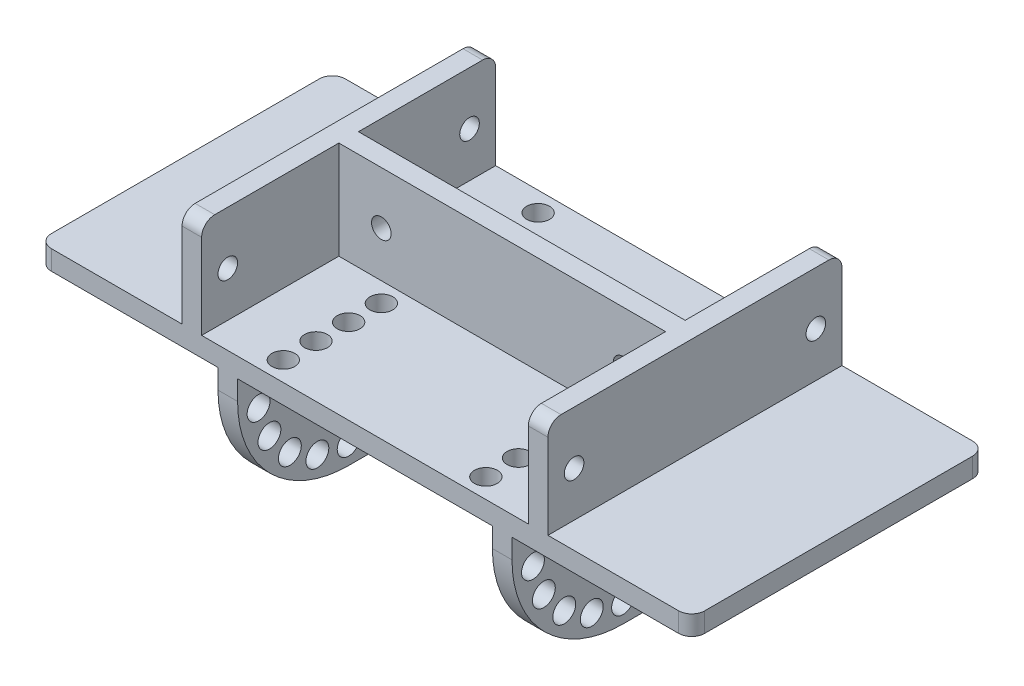
SolidWorks part; units mm, degrees
ref_plane "Front Plane" through (0, 0, 0) normal (0, 0, 1) x (1, 0, 0)
ref_plane "Top Plane" through (0, 0, 0) normal (0, 1, 0) x (1, 0, 0)
ref_plane "Right Plane" through (0, 0, 0) normal (1, 0, 0) x (0, 0, -1)
sketch "Sketch1" plane through (0, 0, 0) normal (0, 1, 0) x (1, 0, 0)
  line L1 (-50, 22.5) -> (50, 22.5)
  line L2 (-50, 22.5) -> (-50, -22.5)
  line L3 (-50, -22.5) -> (50, -22.5)
  line L4 (50, 22.5) -> (50, -22.5)
  line L5 (-50, 22.5) -> (50, -22.5) construction
  line L6 (-50, -22.5) -> (50, 22.5) construction
  point P0 (0, 0)
  dimension "D1" = 100
  dimension "D2" = 45
extrude "Boss-Extrude1" add sketch "Sketch1" along normal blind 3
sketch "Sketch2" plane through (0, 3, 0) normal (0, 1, 0) x (1, 0, 0)
  line L0 (50, 22.5) -> (-50, 22.5) construction
  line L1 (-28, 22.5) -> (-25, 22.5)
  line L2 (-28, 22.5) -> (-28, -22.5)
  line L3 (-28, -22.5) -> (-25, -22.5)
  line L4 (-25, 22.5) -> (-25, -22.5)
  line L5 (-50, -22.5) -> (50, -22.5) construction
  line L6 (-50, 22.5) -> (-50, -22.5) construction
  line L7 (25, 22.5) -> (28, 22.5)
  line L8 (25, 22.5) -> (25, -22.5)
  line L9 (25, -22.5) -> (28, -22.5)
  line L10 (28, 22.5) -> (28, -22.5)
  line L11 (50, -22.5) -> (50, 22.5) construction
  line L13 (-25, 1.5) -> (25, 1.5)
  line L14 (-25, 1.5) -> (-25, -1.5)
  line L15 (-25, -1.5) -> (25, -1.5)
  line L16 (25, 1.5) -> (25, -1.5)
  line M8 (50, 22.5) -> (-50, 22.5)
  line M10 (-50, -22.5) -> (50, -22.5)
  dimension "D1" = 3
  dimension "D2" = 3
  dimension "D3" = 22
  dimension "D4" = 22
  dimension "D5" = 3
  dimension "D6" = 21
extrude "Boss-Extrude2" add sketch "Sketch2" along normal blind 15 contours L4 L15 L8 L13 | L10 L8 M8 M10
sketch "Sketch4" plane through (-28, 0, 0) normal (-1, 0, 0) x (0, 0, 1)
  line L0 (0, 0) -> (0, 9.8851) construction
  line L1 (-18.5, 9.8851) -> (18.5, 9.8851) construction
  circle A0 centre (-18.5, 9.8851) radius 1.5
  circle A1 centre (18.5, 9.8851) radius 1.5
  point P6 (0, 9.8851)
  dimension "D2" = 3
  dimension "D3" = 3
  dimension "D1" = 37
extrude "Cut-Extrude1" cut sketch "Sketch4" against normal through all
sketch "Sketch5" plane through (0, 0, 1.5) normal (0, 0, 1) x (1, 0, 0)
  line L0 (0, 0) -> (0, 9.9635) construction
  line L1 (-18.5, 9.9635) -> (18.5, 9.9635) construction
  circle A0 centre (-18.5, 9.9635) radius 1.5
  circle A1 centre (18.5, 9.9635) radius 1.5
  point P5 (0, 9.9635)
  dimension "D2" = 3
  dimension "D3" = 3
  dimension "D1" = 37
extrude "Cut-Extrude2" cut sketch "Sketch5" against normal through all
fillet "Fillet1" radius 2 8 edges at (-26.5, 18, 22.5) (26.5, 18, 22.5) (26.5, 18, -22.5) (-26.5, 18, -22.5) (50, 1.5, 22.5) (-50, 1.5, 22.5) (-50, 1.5, -22.5) (50, 1.5, -22.5)
sketch "Sketch6" plane through (0, 0, 0) normal (0, -1, 0) x (1, 0, 0)
  line L0 (-19.5, 0) -> (19.5, 0) construction
  line L1 (48, -22.5) -> (-48, -22.5) construction
  line L2 (-19.5, 22.5) -> (-22.5, 22.5)
  line L3 (-19.5, 22.5) -> (-19.5, -22.5)
  line L4 (-19.5, -22.5) -> (-22.5, -22.5)
  line L5 (-22.5, 22.5) -> (-22.5, -22.5)
  line L7 (19.5, 22.5) -> (22.5, 22.5)
  line L8 (19.5, 22.5) -> (19.5, -22.5)
  line L9 (19.5, -22.5) -> (22.5, -22.5)
  line L10 (22.5, 22.5) -> (22.5, -22.5)
  point P3 (0, 0)
  point P14 (0, 0)
  dimension "D1" = 39
  dimension "D2" = 45
  dimension "D3" = 3
  dimension "D4" = 3
  dimension "D5" = 45
extrude "Boss-Extrude3" add sketch "Sketch6" along normal blind 20
fillet "Fillet2" radius 17 4 edges at (21, -20, -22.5) (-21, -20, -22.5) (21, -20, 22.5) (-21, -20, 22.5)
sketch "Sketch7" plane through (22.5, 0, 0) normal (1, 0, 0) x (0, 0, -1)
  line L0 (5.5, -20) -> (5.5, -17) construction
  circle A0 centre (5.5, -17) radius 1.75
  dimension "D2" = 3.5
  dimension "D1" = 3
extrude "Cut-Extrude3" cut sketch "Sketch7" against normal through all
pattern_circular "CirPattern1" count 5 every 20 about axis through (0, -3, -5.5) along (1, 0, 0) of "Cut-Extrude3"
mirror "Mirror1" about plane through (0, 0, 0) normal (0, 0, 1) of "CirPattern1", "Cut-Extrude3"
sketch "Sketch8" plane through (0, 3, 0) normal (0, 1, 0) x (1, 0, 0)
  line L0 (0, 22.5) -> (0, 19.5) construction
  line L1 (25, 22.5) -> (-25, 22.5) construction
  line L2 (-15.5, 19.5) -> (15.5, 19.5) construction
  circle A0 centre (-15.5, 19.5) radius 1.75
  circle A1 centre (15.5, 19.5) radius 1.75
  point P7 (0, 19.5)
  dimension "D3" = 3.5
  dimension "D4" = 3.5
  dimension "D1" = 3
  dimension "D2" = 31
extrude "Cut-Extrude4" cut sketch "Sketch8" against normal through all
pattern_linear "LPattern1" count 4 spacing 5 along (0, 0, 1) of "Cut-Extrude4"
mirror "Mirror2" about plane through (0, 0, 0) normal (0, 0, 1) of "LPattern1", "Cut-Extrude4"
